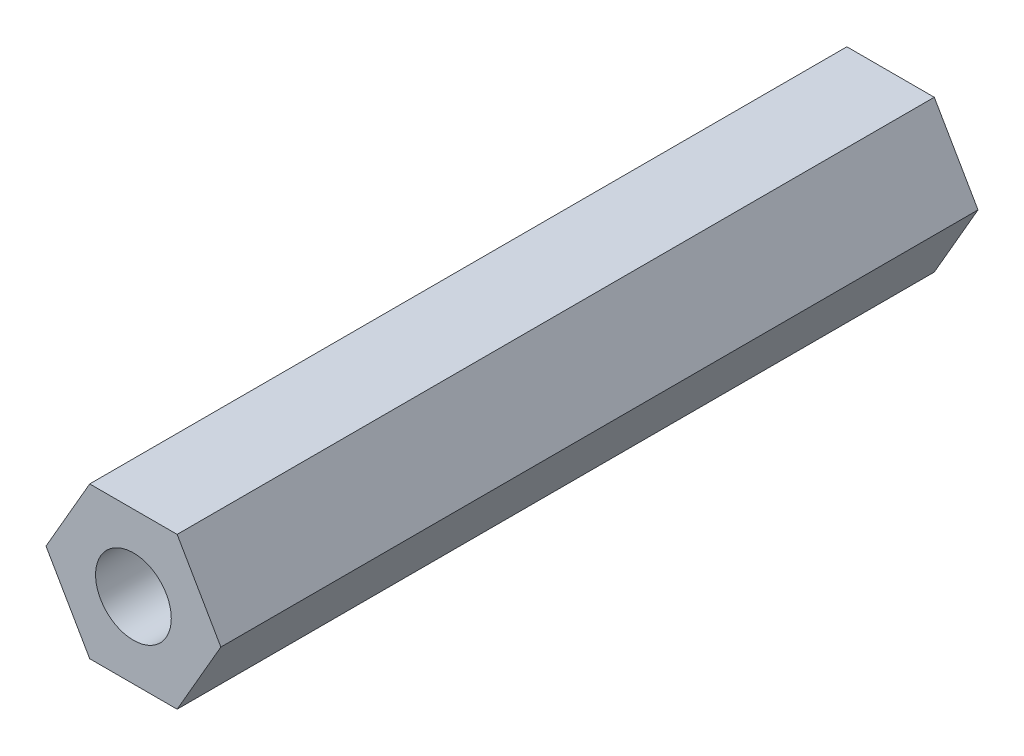
SolidWorks part; units mm, degrees
material "6061 合金"
ref_plane "前视基准面" through (0, 0, 0) normal (0, 0, 1) x (1, 0, 0)
ref_plane "上视基准面" through (0, 0, 0) normal (0, 1, 0) x (1, 0, 0)
ref_plane "右视基准面" through (0, 0, 0) normal (1, 0, 0) x (0, 0, -1)
sketch "草图1" plane through (0, 0, 0) normal (0, 0, 1) x (1, 0, 0)
  line L1 (1.4434, 2.5) -> (-1.4434, 2.5)
  line L2 (-1.4434, 2.5) -> (-2.8868, 0)
  line L3 (-2.8868, 0) -> (-1.4434, -2.5)
  line L4 (-1.4434, -2.5) -> (1.4434, -2.5)
  line L5 (1.4434, -2.5) -> (2.8868, 0)
  line L6 (2.8868, 0) -> (1.4434, 2.5)
  circle A0 centre (0, 0) radius 2.5 construction
  dimension "D1" = 5
extrude "凸台-拉伸1" add sketch "草图1" along normal blind 25
hole_wizard "M3 螺纹孔1" positions "草图2" profile "草图3" tap size "M3" standard "GB" end condition through all
sketch "草图2" plane through (0, 0, 25) normal (0, 0, 1) x (1, 0, 0)
  point P0 (0, 0)
sketch "草图3" plane through (0, 0, 25) normal (1, 0, 0) x (0, -1, 0)
  line L0 (0, 0) -> (0, 25)
  line L1 (0, 25) -> (1.25, 25)
  line L2 (1.25, 25) -> (1.25, 0)
  line L5 (1.25, 0) -> (0, 0)
  line L11 (0, -6.35) -> (0, 107.95) construction
  dimension "通孔螺纹孔钻头直径" = 2.5
  dimension "通孔螺纹孔钻头深度" = 25
cosmetic thread "孔螺蚊线1"
